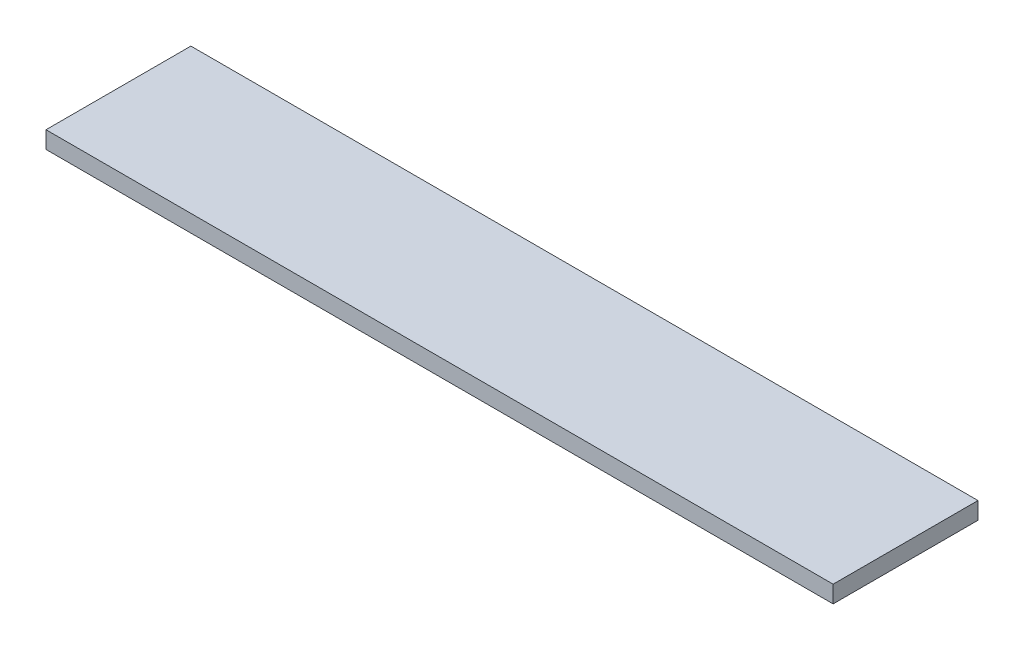
SolidWorks part; units mm, degrees
ref_plane "Front Plane" through (0, 0, 0) normal (0, 0, 1) x (1, 0, 0)
ref_plane "Top Plane" through (0, 0, 0) normal (0, 1, 0) x (1, 0, 0)
ref_plane "Right Plane" through (0, 0, 0) normal (1, 0, 0) x (0, 0, -1)
sketch "Sketch1" plane through (0, 0, 0) normal (0, 1, 0) x (1, 0, 0)
  line L1 (-55.2012, 19.0624) -> (82.7988, 19.0624)
  line L2 (-55.2012, 19.0624) -> (-55.2012, -6.3376)
  line L3 (-55.2012, -6.3376) -> (82.7988, -6.3376)
  line L4 (82.7988, 19.0624) -> (82.7988, -6.3376)
  dimension "D1" = 25.4
  dimension "D2" = 138
extrude "Boss-Extrude1" add sketch "Sketch1" along normal blind 3
